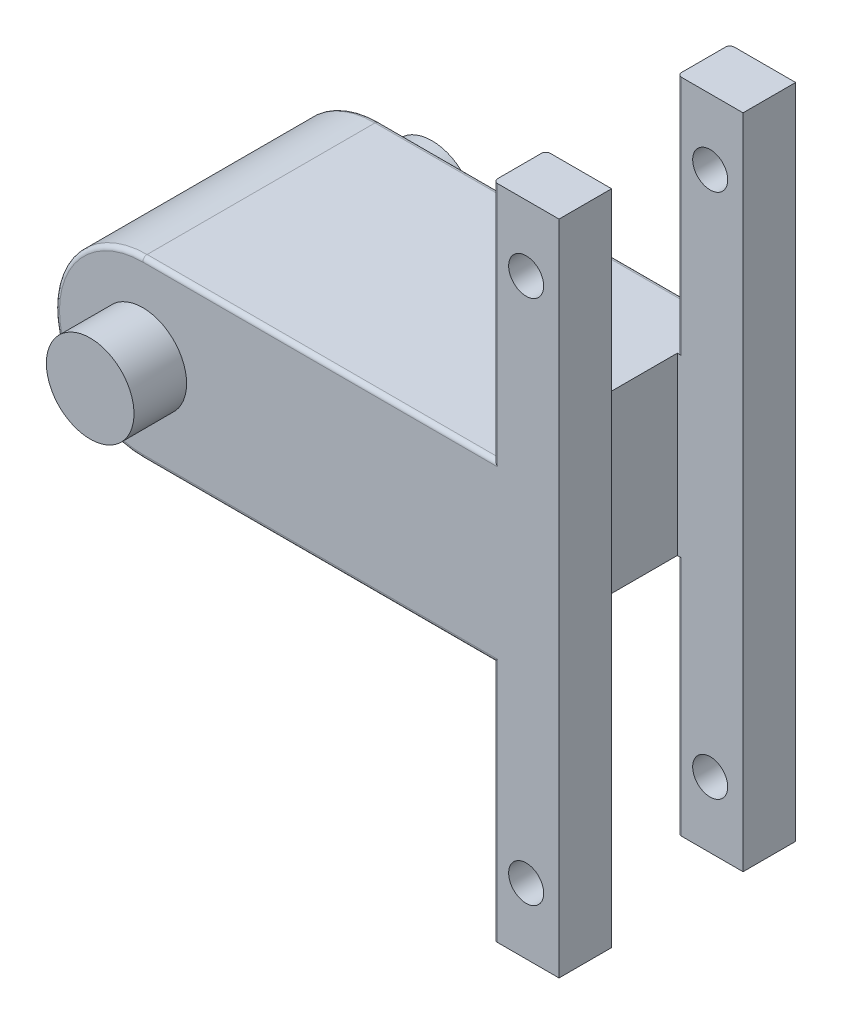
SolidWorks part; units mm, degrees
ref_plane "Front Plane" through (0, 0, 0) normal (0, 0, 1) x (1, 0, 0)
ref_plane "Top Plane" through (0, 0, 0) normal (0, 1, 0) x (1, 0, 0)
ref_plane "Right Plane" through (0, 0, 0) normal (1, 0, 0) x (0, 0, -1)
sketch "Sketch1" plane through (0, 0, 0) normal (0, 0, 1) x (1, 0, 0)
  line L1 (0, 75) -> (0, 20)
  line L2 (0, 75) -> (15, 75)
  line L3 (15, 75) -> (15, -75)
  line L4 (15, -75) -> (0, -75)
  line L5 (-80, 20) -> (0, 20)
  line L6 (-80, -20) -> (0, -20)
  line L7 (0, -20) -> (0, -75)
  arc A0 (-80, 20) -> (-80, -20) centre (-80, 0) ccw
  circle A1 centre (7.5, 60) radius 4
  circle A2 centre (7.5, -60) radius 4
  point P7 (0, 0)
  point P15 (7.5, -75)
  dimension "D2" = 40
  dimension "D1" = 8
  dimension "D6" = 8
  dimension "D3" = 150
  dimension "D4" = 15
  dimension "D5" = 15
  dimension "D7" = 15
extrude "Boss-Extrude1" add sketch "Sketch1" along normal blind 54
sketch "Sketch2" plane through (0, 0, 0) normal (0, 0, -1) x (-1, 0, 0)
  circle A0 centre (80, 0) radius 10
  dimension "D1" = 20
extrude "Boss-Extrude2" add sketch "Sketch2" along normal blind 12
ref_plane "Plane1" through (0, 0, 27) normal (0, 0, 1) x (1, 0, 0)
mirror "Mirror1" about plane through (0, 0, 27) normal (0, 0, 1) of "Boss-Extrude2"
sketch "Sketch3" plane through (0, 75, 0) normal (0, 1, 0) x (1, 0, 0)
  line L0 (15, -27) -> (0, -27) construction
  line L1 (15, -54) -> (15, 0) construction
  line L2 (0, -54) -> (0, 0) construction
  line L3 (0, -54) -> (0, 0) construction
  line L4 (15, -12) -> (0, -12)
  line L5 (15, -12) -> (15, -42)
  line L6 (15, -42) -> (0, -42)
  line L7 (0, -12) -> (0, -42)
  line L8 (15, -12) -> (0, -42) construction
  line L9 (15, -42) -> (0, -12) construction
  point P6 (7.5, -27)
  dimension "D1" = 30
extrude "Cut-Extrude1" cut sketch "Sketch3" against normal blind 150
fillet "Fillet1" radius 1 14 edges at (-40, -20, 0) (-100, 0, 0) (-40, -20, 54) (-100, 0, 54) (0, -47.5, 0) (0, -47.5, 12) (0, -47.5, 42) (0, -47.5, 54) (0, 47.5, 54) (0, 47.5, 42) (0, 47.5, 12) (0, 47.5, 0) (-40, 20, 0) (-40, 20, 54)
